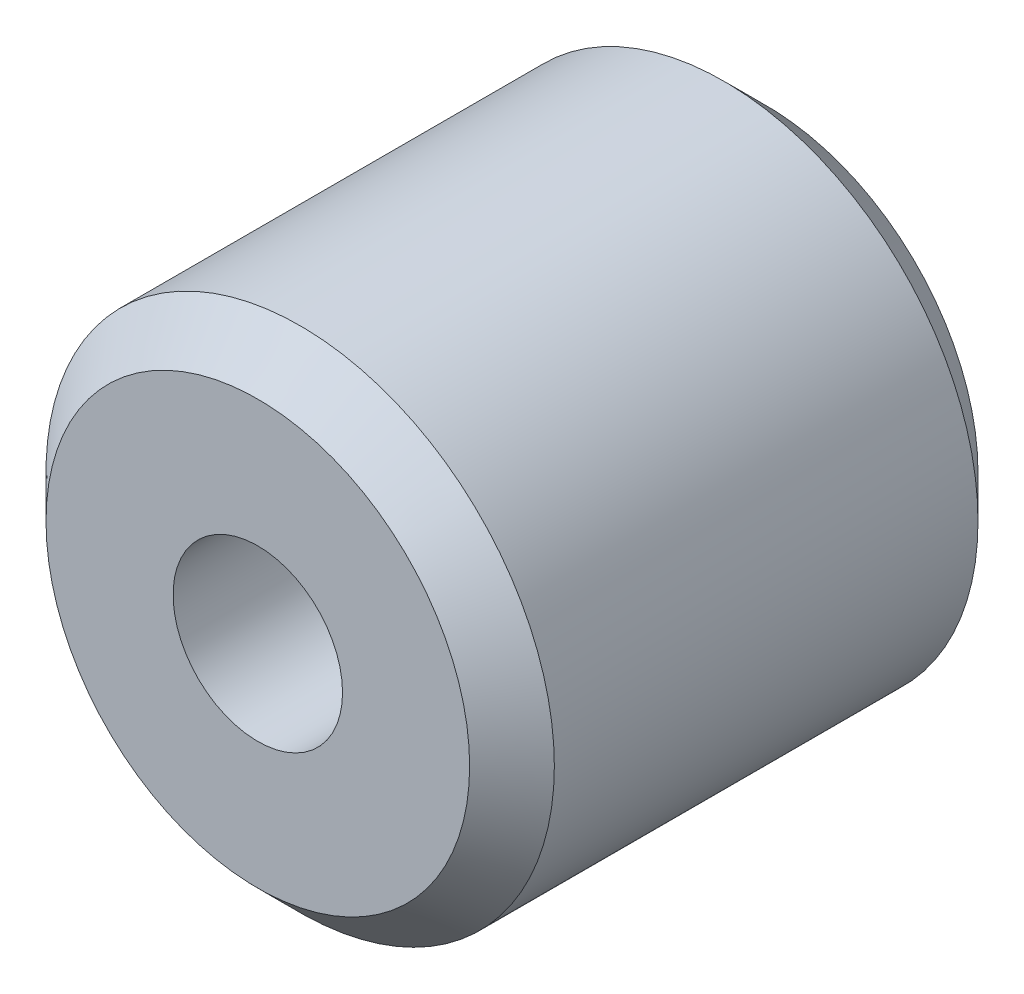
SolidWorks part; units mm, degrees
material "ABS"
ref_plane "Front Plane" through (0, 0, 0) normal (0, 0, 1) x (1, 0, 0)
ref_plane "Top Plane" through (0, 0, 0) normal (0, 1, 0) x (1, 0, 0)
ref_plane "Right Plane" through (0, 0, 0) normal (1, 0, 0) x (0, 0, -1)
sketch "Sketch1" plane through (0, 0, 0) normal (0, 0, 1) x (1, 0, 0)
  circle A0 centre (0, 0) radius 6
  dimension "D1" = 12
extrude "Boss-Extrude1" add sketch "Sketch1" along normal blind 12
sketch "Sketch2" plane through (0, 0, 0) normal (0, 0, 1) x (1, 0, 0)
  circle A0 centre (0, 0) radius 2
  dimension "D1" = 4
extrude "Cut-Extrude1" cut sketch "Sketch2" along normal through all
chamfer "Chamfer1" distance 1 angle 45 2 edges at (6, 0, 0) (6, 0, 12)
